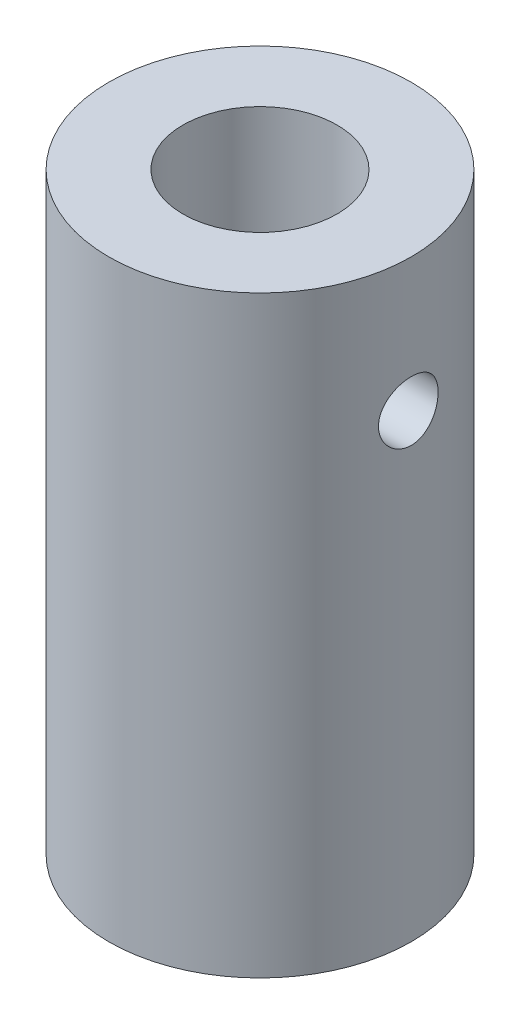
SolidWorks part; units mm, degrees
ref_plane "Front Plane" through (0, 0, 0) normal (0, 0, 1) x (1, 0, 0)
ref_plane "Top Plane" through (0, 0, 0) normal (0, 1, 0) x (1, 0, 0)
ref_plane "Right Plane" through (0, 0, 0) normal (1, 0, 0) x (0, 0, -1)
sketch "Sketch1" plane through (0, 0, 0) normal (0, 1, 0) x (1, 0, 0)
  circle A0 centre (0, 0) radius 12.954
  circle A1 centre (0, 0) radius 6.604
  dimension "D1" = 25.908
  dimension "D2" = 6.35
extrude "Boss-Extrude1" add sketch "Sketch1" along normal blind 50.8
sketch "Sketch2" plane through (0, 0, 0) normal (1, 0, 0) x (0, 0, -1)
  point P0 (0, 39.37)
  dimension "D1" = 39.37
hole_wizard "1/4-20 Tapped Hole1" positions "Sketch2" profile "Sketch3" tap size "1/4-20" standard "ANSI Inch"
sketch "Sketch3" plane through (0, 39.37, 0) normal (0, 1, 0) x (0, 0, 1)
  line L0 (0, 0) -> (0, 12.954)
  line L1 (0, 12.954) -> (2.5527, 12.954)
  line L2 (2.5527, 12.954) -> (2.5527, 0)
  line L5 (2.5527, 0) -> (0, 0)
  line L11 (0, -6.35) -> (0, 107.95) construction
  dimension "Thru Tap Drill Dia." = 5.1054
  dimension "Thru Tap Drill Depth" = 12.954
cosmetic thread "Hole Thread1" parameters "D2"=6.35
